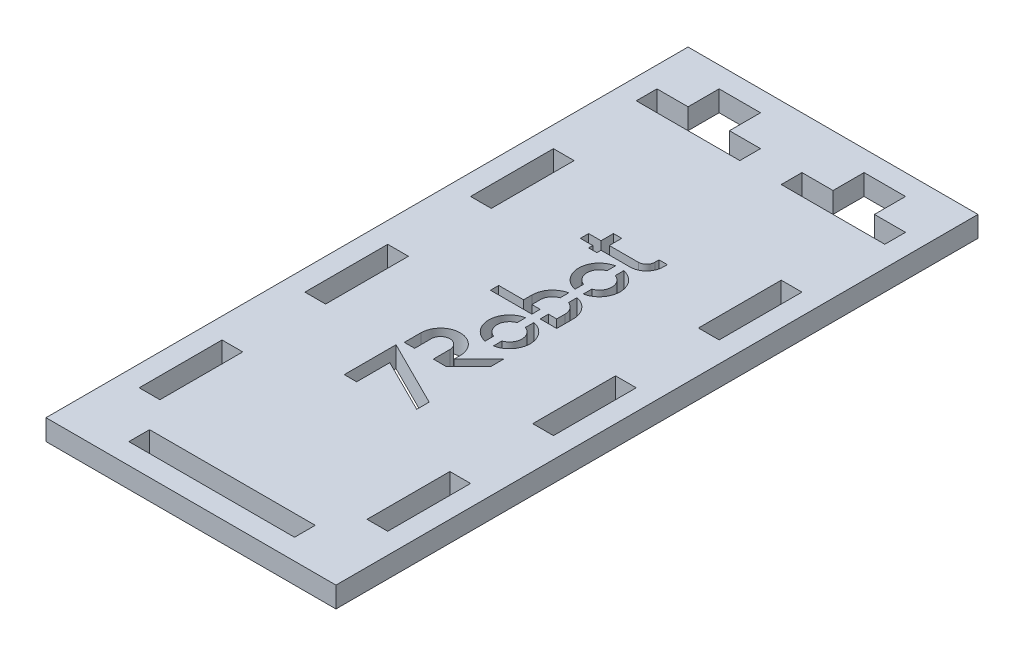
SolidWorks part; units mm, degrees
ref_plane "Plan de face" through (0, 0, 0) normal (0, 0, 1) x (1, 0, 0)
ref_plane "Plan de dessus" through (0, 0, 0) normal (0, 1, 0) x (1, 0, 0)
ref_plane "Plan de droite" through (0, 0, 0) normal (1, 0, 0) x (0, 0, -1)
sketch "Esquisse1" plane through (0, 0, 0) normal (0, 1, 0) x (1, 0, 0)
  line L0 (-22.5, 77.5) -> (-12.5, 77.5)
  line L1 (-12.5, 77.5) -> (-12.5, 70)
  line L2 (25, 45) -> (30, 45)
  line L3 (-30, 45) -> (-25, 45)
  line L4 (-30, 45) -> (-30, 25)
  line L5 (-35, 82.5) -> (35, 82.5)
  line L6 (-35, 82.5) -> (-35, -72.5)
  line L7 (-35, -72.5) -> (35, -72.5)
  line L8 (35, 82.5) -> (35, -72.5)
  line L9 (-12.5, 70) -> (-5, 70)
  line L10 (-5, 70) -> (-5, 65)
  line L11 (-5, 65) -> (-30, 65)
  line L12 (-30, 65) -> (-30, 70)
  line L13 (-30, 70) -> (-22.5, 70)
  line L14 (-22.5, 70) -> (-22.5, 77.5)
  line L15 (12.5, 77.5) -> (22.5, 77.5)
  line L16 (22.5, 77.5) -> (22.5, 70)
  line L17 (22.5, 70) -> (30, 70)
  line L18 (30, 70) -> (30, 65)
  line L19 (30, 65) -> (5, 65)
  line L20 (5, 65) -> (5, 70)
  line L21 (5, 70) -> (12.5, 70)
  line L22 (12.5, 70) -> (12.5, 77.5)
  line L23 (-30, 25) -> (-25, 25)
  line L24 (-25, 45) -> (-25, 25)
  line L25 (-30, 5) -> (-25, 5)
  line L26 (-30, 5) -> (-30, -15)
  line L27 (-30, -15) -> (-25, -15)
  line L28 (-25, 5) -> (-25, -15)
  line L29 (-30, -35) -> (-25, -35)
  line L30 (-30, -35) -> (-30, -55)
  line L31 (-30, -55) -> (-25, -55)
  line L32 (-25, -35) -> (-25, -55)
  line L33 (25, 45) -> (25, 25)
  line L34 (25, 25) -> (30, 25)
  line L35 (30, 45) -> (30, 25)
  line L36 (25, 5) -> (30, 5)
  line L37 (25, 5) -> (25, -15)
  line L38 (25, -15) -> (30, -15)
  line L39 (30, 5) -> (30, -15)
  line L40 (25, -35) -> (30, -35)
  line L41 (25, -35) -> (25, -55)
  line L42 (25, -55) -> (30, -55)
  line L43 (30, -35) -> (30, -55)
  line L45 (-20, -62.5) -> (20, -62.5)
  line L46 (-20, -62.5) -> (-20, -67.5)
  line L47 (-20, -67.5) -> (20, -67.5)
  line L48 (20, -62.5) -> (20, -67.5)
  dimension "D1" = 10
  dimension "D3" = 35
  dimension "D4" = 5
  dimension "D5" = 82.5
  dimension "D6" = 20
  dimension "D7" = 70
  dimension "D8" = 155
  dimension "D9" = 7.5
  dimension "D10" = 7.5
  dimension "D11" = 5
  dimension "D12" = 25
  dimension "D13" = 5
  dimension "D14" = 5
  dimension "D15" = 5
  dimension "D16" = 7.5
  dimension "D17" = 7.5
  dimension "D18" = 25
  dimension "D19" = 5
  dimension "D20" = 5
  dimension "D21" = 5
  dimension "D22" = 5
  dimension "D23" = 10
  dimension "D24" = 5
  dimension "D25" = 5
  dimension "D26" = 20
  dimension "D27" = 20
  dimension "D28" = 20
  dimension "D29" = 5
  dimension "D30" = 20
  dimension "D31" = 5
  dimension "D32" = 20
  dimension "D33" = 5
  dimension "D34" = 5
  dimension "D35" = 5
  dimension "D36" = 5
  dimension "D37" = 20
  dimension "D38" = 20
  dimension "D39" = 20
  dimension "D40" = 20
  dimension "D41" = 20
  dimension "D42" = 20
  dimension "D43" = 5
  dimension "D44" = 5
  dimension "D45" = 5
  dimension "D46" = 40
  dimension "D47" = 15
  dimension "D48" = 5
  dimension "D49" = 5
extrude "Boss.-Extru.1" add sketch "Esquisse1" along normal blind 5
sketch "Esquisse2" plane through (0, 5, 0) normal (0, 1, 0) x (1, 0, 0)
  line L0 (-8, -27.5) -> (-5, -27.5)
  line L1 (-5, -27.5) -> (-5, -19.5)
  line L2 (-5, -19.5) -> (8, -26)
  line L3 (8, -26) -> (8, -23)
  line L4 (8, -23) -> (-8, -15)
  line L5 (-8, -15) -> (-8, -27.5)
  line L6 (8, -5) -> (8, -8)
  line L7 (8, -8) -> (2.5, -13.5)
  line L8 (2.5, -13.5) -> (-0.5, -13.5)
  line L9 (-0.5, -13.5) -> (-0.5, -9.5)
  line L10 (-7.5, -13.5) -> (-5, -13.5)
  line L11 (-5, -13.5) -> (-5, -9.5)
  line L12 (-7.5, -13.5) -> (-7.5, -9.5)
  line L13 (8, -5) -> (2, -11)
  line L14 (2, -9.5) -> (2, -11)
  line L15 (35, -72.5) -> (35, 82.5) construction
  line L16 (-35, -72.5) -> (35, -72.5) construction
  line L17 (2, -3.5) -> (2, -1.4294)
  line L18 (2, 4.2274) -> (2, 6.298)
  line L19 (4, 6.298) -> (4, 4.2274)
  line L20 (4, -1.4294) -> (4, -3.5)
  line L21 (-8, 7.798) -> (2, 7.798)
  line L22 (2, 7.798) -> (2, 9.798)
  line L23 (-2, 9.798) -> (-2, 11.798)
  line L24 (-8, 7.798) -> (-8, 9.798)
  line L25 (-8, 9.798) -> (-2, 9.798)
  line L26 (4, 7.798) -> (8, 7.798)
  line L27 (8, 7.798) -> (8, 11.798)
  line L28 (4, 7.798) -> (4, 9.798)
  line L29 (2, 9.798) -> (0, 9.798)
  line L30 (0, 9.798) -> (0, 11.798)
  line L31 (4, 9.798) -> (6, 9.798)
  line L32 (6, 11.798) -> (6, 9.798)
  line L33 (2, 14.6264) -> (2, 16.6969)
  line L34 (4, 16.6969) -> (4, 14.6264)
  line L35 (2, 18.1969) -> (2, 20.2675)
  line L36 (2, 25.9243) -> (2, 27.9949)
  line L37 (4, 27.9949) -> (4, 25.9243)
  line L38 (4, 20.2675) -> (4, 18.1969)
  line L39 (-8, 29.4949) -> (-5, 29.4949)
  line L40 (-8, 29.4949) -> (-8, 31.4949)
  line L41 (-8, 31.4949) -> (-5, 31.4949)
  line L42 (-5, 31.4949) -> (-5, 34.4949)
  line L43 (-5, 34.4949) -> (-3, 34.4949)
  line L44 (-3, 34.4949) -> (-3, 31.4949)
  line L45 (-3, 31.4949) -> (4, 31.4949)
  line L46 (6, 33.4949) -> (6, 34.4949)
  line L47 (6, 34.4949) -> (8, 34.4949)
  line L48 (8, 34.4949) -> (8, 33.4949)
  line L49 (-5, 29.4949) -> (-5, 28.4949)
  line L50 (-5, 28.4949) -> (-3, 28.4949)
  line L51 (-3, 28.4949) -> (-3, 29.4949)
  line L52 (-3, 29.4949) -> (4, 29.4949)
  arc A0 (-5, -9.5) -> (-0.5, -9.5) centre (-2.75, -9.5) cw
  arc A1 (-7.5, -9.5) -> (2, -9.5) centre (-2.75, -9.5) cw
  arc A2 (2, -3.5) -> (2, 6.298) centre (3, 1.399) cw
  arc A3 (2, -1.4294) -> (2, 4.2274) centre (3, 1.399) cw
  arc A4 (4, 4.2274) -> (4, -1.4294) centre (3, 1.399) cw
  arc A5 (4, 6.298) -> (4, -3.5) centre (3, 1.399) cw
  arc A6 (0, 11.798) -> (2, 14.6264) centre (3, 11.798) cw
  arc A7 (6, 11.798) -> (4, 14.6264) centre (3, 11.798) ccw
  arc A8 (-2, 11.798) -> (2, 16.6969) centre (3, 11.798) cw
  arc A9 (8, 11.798) -> (4, 16.6969) centre (3, 11.798) ccw
  arc A10 (2, 18.1969) -> (2, 27.9949) centre (3, 23.0959) cw
  arc A11 (2, 20.2675) -> (2, 25.9243) centre (3, 23.0959) cw
  arc A12 (4, 25.9243) -> (4, 20.2675) centre (3, 23.0959) cw
  arc A13 (4, 27.9949) -> (4, 18.1969) centre (3, 23.0959) cw
  arc A14 (4, 29.4949) -> (8, 33.4949) centre (4, 33.4949) ccw
  arc A15 (4, 31.4949) -> (6, 33.4949) centre (4, 33.4949) ccw
  dimension "D14" = 5
  dimension "D15" = 3
  dimension "D16" = 3
  dimension "D17" = 5
  dimension "D33" = 3
  dimension "D34" = 5
  dimension "D35" = 3
  dimension "D36" = 5
  dimension "D39" = 3
  dimension "D40" = 1.5
  dimension "D56" = 3
  dimension "D1" = 3
  dimension "D2" = 8
  dimension "D3" = 13
  dimension "D4" = 2.5
  dimension "D5" = 3
  dimension "D6" = 4.5
  dimension "D7" = 4
  dimension "D8" = 3
  dimension "D9" = 3
  dimension "D10" = 12.5
  dimension "D11" = 4
  dimension "D12" = 27
  dimension "D13" = 5
  dimension "D18" = 45
  dimension "D19" = 1.5
  dimension "D20" = 2
  dimension "D21" = 2
  dimension "D22" = 4
  dimension "D23" = 2
  dimension "D24" = 2
  dimension "D25" = 2
  dimension "D26" = 2
  dimension "D27" = 2
  dimension "D28" = 4
  dimension "D29" = 2
  dimension "D30" = 1.5
  dimension "D31" = 2
  dimension "D32" = 2
  dimension "D37" = 2
  dimension "D38" = 5.5
  dimension "D41" = 13
  dimension "D42" = 2
  dimension "D43" = 2
  dimension "D44" = 1
  dimension "D45" = 3
  dimension "D46" = 2
  dimension "D47" = 2
  dimension "D48" = 2
  dimension "D49" = 1.5
  dimension "D50" = 4
  dimension "D51" = 4
  dimension "D52" = 2
  dimension "D53" = 2
  dimension "D54" = 1
  dimension "D55" = 4
  dimension "D57" = 2
  dimension "D58" = 4
  dimension "D59" = 10
  dimension "D60" = 4
  dimension "D61" = 1.5
  dimension "D62" = 1.5
  dimension "D63" = 4
  dimension "D64" = 2
  dimension "D65" = 7
  dimension "D66" = 7
  dimension "D67" = 2
  dimension "D68" = 3
  dimension "D69" = 4
  dimension "D70" = 3
  dimension "D71" = 1
extrude "Enlèv. mat.-Extru.1" cut sketch "Esquisse2" against normal blind 5
